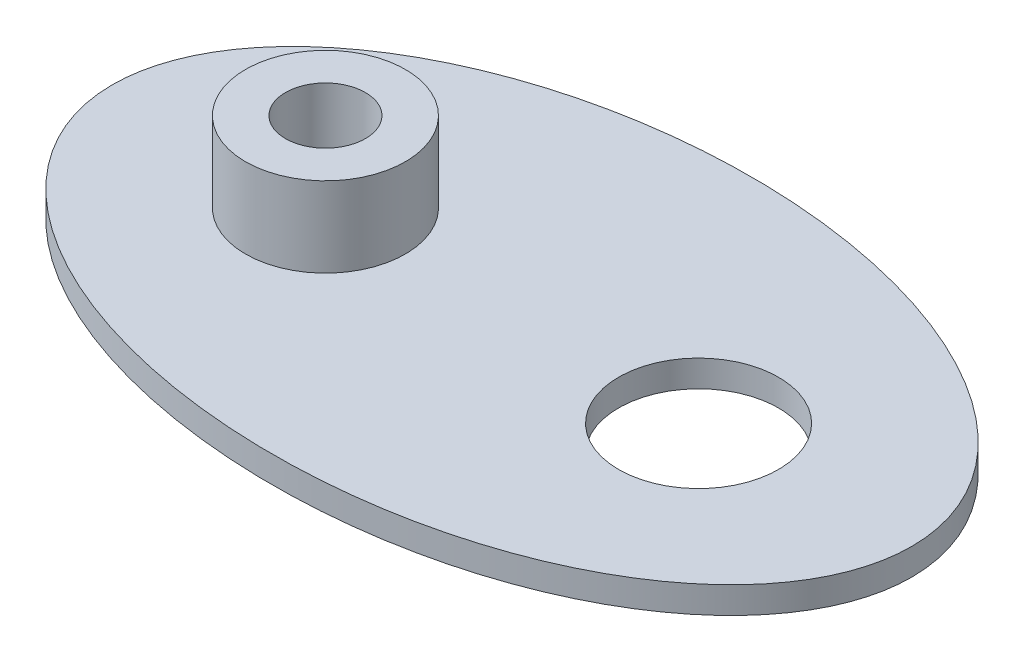
SolidWorks part; units mm, degrees
ref_plane "Alzado" through (0, 0, 0) normal (0, 0, 1) x (1, 0, 0)
ref_plane "Planta" through (0, 0, 0) normal (0, 1, 0) x (1, 0, 0)
ref_plane "Vista lateral" through (0, 0, 0) normal (1, 0, 0) x (0, 0, -1)
sketch "Croquis1" plane through (0, 0, 0) normal (0, 1, 0) x (1, 0, 0)
  line L0 (-15, 0) -> (15, 0) construction
  circle A0 centre (-7, 0) radius 3
  circle A1 centre (7, 0) radius 3
  ellipse E0 centre (0, 0) end of major axis (-15, 0) minor radius 9
  dimension "D1" = 8
  dimension "D2" = 8
extrude "Saliente-Extruir1" add sketch "Croquis1" along normal blind 1
sketch "Croquis2" plane through (0, 1, 0) normal (0, 1, 0) x (1, 0, 0)
  circle A0 centre (-7, 0) radius 1.5
  circle A1 centre (-7, 0) radius 3 construction
  circle A2 centre (-7, 0) radius 3
extrude "Saliente-Extruir2" add sketch "Croquis2" along normal blind 3
